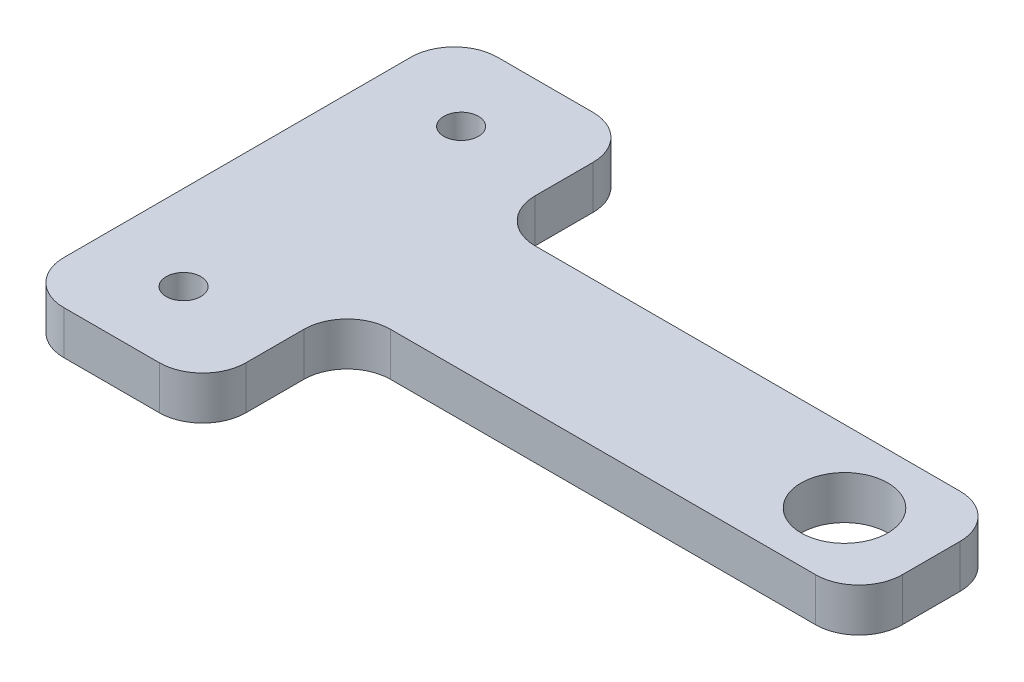
SolidWorks part; units mm, degrees
material "ABS"
ref_plane "Front Plane" through (0, 0, 0) normal (0, 0, 1) x (1, 0, 0)
ref_plane "Top Plane" through (0, 0, 0) normal (0, 1, 0) x (1, 0, 0)
ref_plane "Right Plane" through (0, 0, 0) normal (1, 0, 0) x (0, 0, -1)
sketch "Sketch1" plane through (0, 0, 0) normal (0, 1, 0) x (1, 0, 0)
  line L0 (1.0526, 25) -> (10.5, 25)
  line L1 (0, 0) -> (40, 0)
  line L2 (0, 0) -> (0, 25)
  line L3 (0, 25) -> (40, 25)
  line L4 (40, 0) -> (40, 25)
  line L5 (10.5, 25) -> (10.5, 0)
  line L6 (10.5, 0) -> (0, 0)
  line L8 (40, 0) -> (10.5, 0)
  line L9 (40, 0) -> (40, 8.3333)
  line L10 (40, 8.3333) -> (10.5, 8.3333)
  line L11 (10.5, 0) -> (10.5, 8.3333)
  line L12 (40, 25) -> (10.5, 25)
  line L13 (40, 25) -> (40, 16.6667)
  line L14 (40, 16.6667) -> (10.5, 16.6667)
  line L15 (10.5, 25) -> (10.5, 16.6667)
  circle A0 centre (4.9, 20.5) radius 1
  circle A1 centre (4.9, 4.5) radius 1
  circle A2 centre (35, 12.5) radius 2.5
  dimension "D5" = 2
  dimension "D6" = 2
  dimension "D11" = 5
  dimension "D1" = 25
  dimension "D2" = 10.5
  dimension "D3" = 40
  dimension "D4" = 16
  dimension "D7" = 4.5
  dimension "D8" = 4.9
  dimension "D9" = 12.5
  dimension "D10" = 5
  dimension "D12" = 8.3333
  dimension "D13" = 8.3333
extrude "Boss-Extrude1" add sketch "Sketch1" along normal blind 2.5 contours L4 L14 L5 L10 A2 | L5 L0 L3 L2 L1 A1 A0
fillet "Fillet1" radius 2.5 8 edges at (40, 1.25, -16.6667) (40, 1.25, -8.3333) (10.5, 1.25, -8.3333) (10.5, 1.25, -16.6667) (10.5, 1.25, -25) (0, 1.25, -25) (0, 1.25, 0) (10.5, 1.25, 0)
